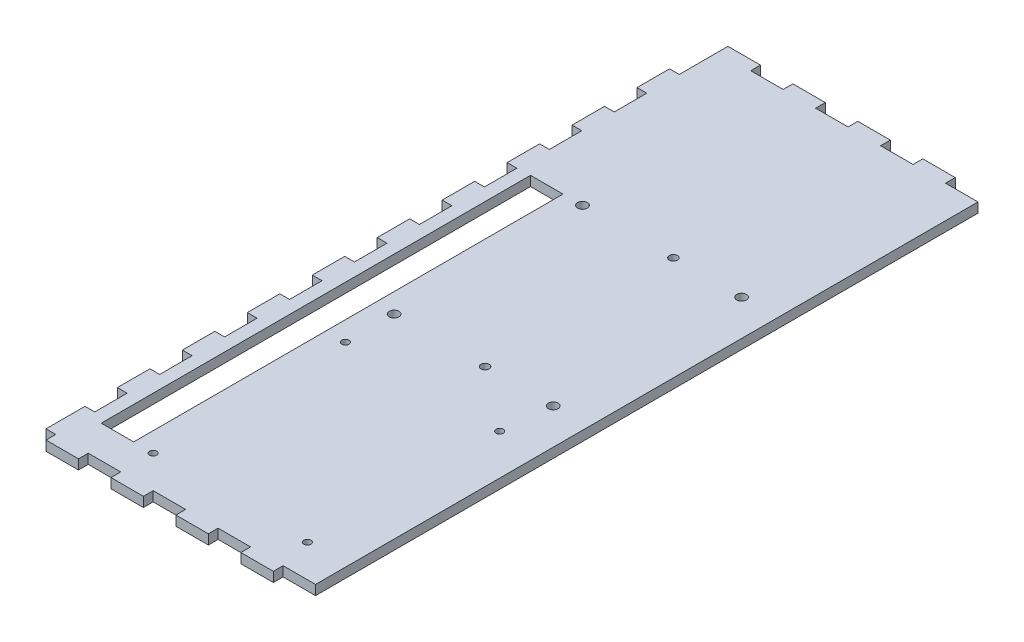
SolidWorks part; units mm, degrees
ref_plane "Front Plane" through (0, 0, 0) normal (0, 0, 1) x (1, 0, 0)
ref_plane "Top Plane" through (0, 0, 0) normal (0, 1, 0) x (1, 0, 0)
ref_plane "Right Plane" through (0, 0, 0) normal (1, 0, 0) x (0, 0, -1)
sketch "Sketch1" plane through (0, 0, 0) normal (0, 1, 0) x (1, 0, 0)
  line L1 (0, 0) -> (80, 0)
  line L2 (0, 0) -> (0, 204)
  line L3 (0, 204) -> (80, 204)
  line L4 (80, 0) -> (80, 204)
  dimension "D1" = 80
  dimension "D2" = 204
extrude "Boss-Extrude1" add sketch "Sketch1" along normal blind 3
sketch "Sketch2" plane through (0, 0, 0) normal (0, 0, 1) x (1, 0, 0)
  line L0 (0, 3) -> (80, 3) construction
  line L1 (0, 0) -> (10, 0)
  line L2 (0, 0) -> (0, 3)
  line L3 (0, 3) -> (10, 3)
  line L4 (10, 0) -> (10, 3)
  dimension "D1" = 10
extrude "Boss-Extrude2" add sketch "Sketch2" along normal blind 3
pattern_linear "LPattern1" count 4 spacing 20 along (1, 0, 0) of "Boss-Extrude2"
sketch "Sketch3" plane through (0, 0, -204) normal (0, 0, -1) x (-1, 0, 0)
  line L0 (-80, 0) -> (0, 0) construction
  line L1 (0, 3) -> (-10, 3)
  line L2 (0, 3) -> (0, 0)
  line L3 (0, 0) -> (-10, 0)
  line L4 (-10, 3) -> (-10, 0)
  dimension "D1" = 10
extrude "Boss-Extrude3" add sketch "Sketch3" along normal blind 3
pattern_linear "LPattern2" count 4 spacing 20 along (1, 0, 0) of "Boss-Extrude3"
sketch "Sketch4" plane through (0, 3, 0) normal (0, 1, 0) x (1, 0, 0)
  line L0 (10, 0) -> (20, 0) construction
  line L2 (0, 207) -> (0, -3) construction
  line L3 (4, 142.2) -> (14, 142.2)
  line L4 (4, 142.2) -> (4, 10)
  line L5 (4, 10) -> (14, 10)
  line L6 (14, 142.2) -> (14, 10)
  circle A0 centre (20, 10) radius 1.1
  circle A1 centre (67.5, 10) radius 1.1
  circle A2 centre (20, 69.2) radius 1.1
  circle A3 centre (67.5, 69.2) radius 1.1
  circle A4 centre (20, 84.2) radius 1.5
  circle A5 centre (69, 84.2) radius 1.5
  circle A6 centre (69, 142.2) radius 1.5
  circle A7 centre (20, 142.2) radius 1.5
  circle A8 centre (48, 84.2) radius 1.25
  circle A9 centre (48, 142.2) radius 1.25
  point P28 (0, 0)
  point P29 (0, 0)
  point P30 (0, 0)
  point P31 (0, 0)
  point P32 (0, 0)
  dimension "D1" = 2.2
  dimension "D8" = 3
  dimension "D13" = 2.5
  dimension "D2" = 59.2
  dimension "D3" = 10
  dimension "D4" = 47.5
  dimension "D5" = 20
  dimension "D6" = 49
  dimension "D7" = 58
  dimension "D9" = 15
  dimension "D10" = 20
  dimension "D11" = 4
  dimension "D12" = 10
  dimension "D14" = 21
extrude "Cut-Extrude1" cut sketch "Sketch4" against normal through all
sketch "Sketch5" plane through (0, 0, 0) normal (-1, 0, 0) x (0, 0, 1)
  line L0 (-207, 3) -> (3, 3) construction
  line L1 (0, 0) -> (-12, 0)
  line L2 (0, 0) -> (0, 3)
  line L3 (0, 3) -> (-12, 3)
  line L4 (-12, 0) -> (-12, 3)
  line L5 (-207, 0) -> (3, 0) construction
  line L6 (-22, 0) -> (-32, 0)
  line L7 (-22, 0) -> (-22, 3)
  line L8 (-22, 3) -> (-32, 3)
  line L9 (-32, 0) -> (-32, 3)
  line L10 (-42, 0) -> (-42, 3)
  line L11 (-42, 0) -> (-52, 0)
  line L12 (-52, 0) -> (-52, 3)
  line L13 (-42, 3) -> (-52, 3)
  line L14 (-62, 0) -> (-62, 3)
  line L15 (-62, 0) -> (-72, 0)
  line L16 (-72, 0) -> (-72, 3)
  line L17 (-62, 3) -> (-72, 3)
  line L18 (-82, 0) -> (-82, 3)
  line L19 (-82, 0) -> (-92, 0)
  line L20 (-92, 0) -> (-92, 3)
  line L21 (-82, 3) -> (-92, 3)
  line L22 (-102, 0) -> (-102, 3)
  line L23 (-102, 0) -> (-112, 0)
  line L24 (-112, 0) -> (-112, 3)
  line L25 (-102, 3) -> (-112, 3)
  line L26 (-122, 0) -> (-122, 3)
  line L27 (-122, 0) -> (-132, 0)
  line L28 (-132, 0) -> (-132, 3)
  line L29 (-122, 3) -> (-132, 3)
  line L30 (-142, 0) -> (-142, 3)
  line L31 (-142, 0) -> (-152, 0)
  line L32 (-152, 0) -> (-152, 3)
  line L33 (-142, 3) -> (-152, 3)
  line L34 (-162, 0) -> (-162, 3)
  line L35 (-162, 0) -> (-172, 0)
  line L36 (-172, 0) -> (-172, 3)
  line L37 (-162, 3) -> (-172, 3)
  line L38 (-182, 0) -> (-182, 3)
  line L39 (-182, 0) -> (-192, 0)
  line L40 (-192, 0) -> (-192, 3)
  line L41 (-182, 3) -> (-192, 3)
  point P13 (-12, 1.5)
  dimension "D1" = 12
  dimension "D2" = 10
  dimension "D3" = 10
  dimension "D4" = 9
extrude "Boss-Extrude4" add sketch "Sketch5" along normal blind 3
